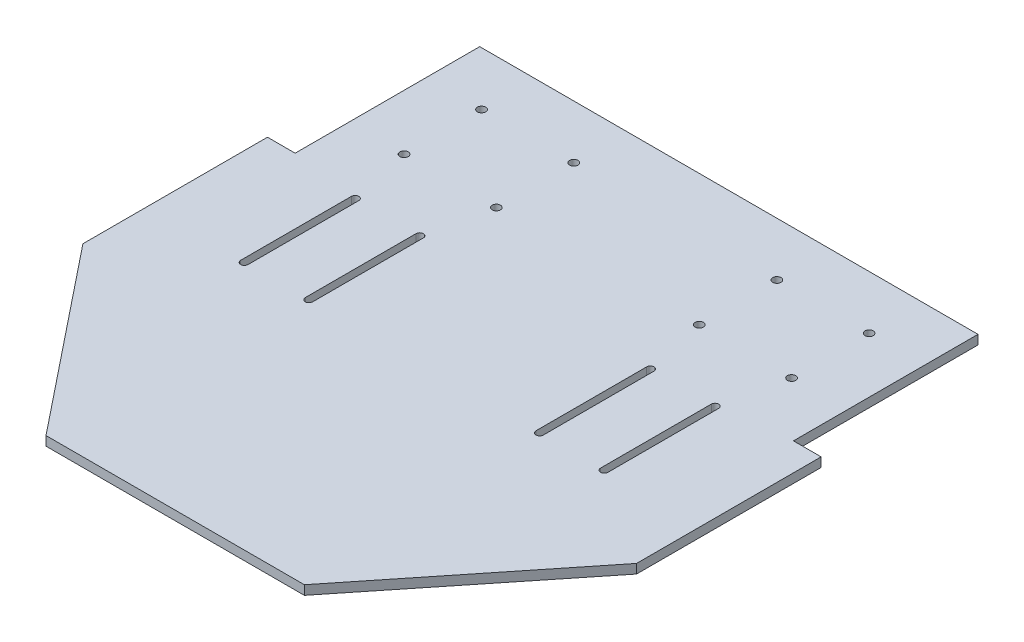
SolidWorks part; units mm, degrees
ref_plane "前基準面" through (0, 0, 0) normal (0, 0, 1) x (1, 0, 0)
ref_plane "上基準面" through (0, 0, 0) normal (0, 1, 0) x (1, 0, 0)
ref_plane "右基準面" through (0, 0, 0) normal (1, 0, 0) x (0, 0, -1)
sketch "草圖2" plane through (0, 0, 0) normal (0, 1, 0) x (1, 0, 0)
  line L0 (0, 150) -> (0, 0) construction
  line L1 (-150, 150) -> (150, 150)
  line L2 (-150, 150) -> (-150, -50)
  line L3 (-70, -150) -> (70, -150)
  line L4 (150, 150) -> (150, -50)
  line L5 (-150, 150) -> (150, -150) construction
  line L6 (-150, -150) -> (150, 150) construction
  line L7 (-105, 121) -> (-55, 121) construction
  line L8 (-105, 121) -> (-105, 79) construction
  line L9 (-105, 79) -> (-55, 79) construction
  line L10 (-55, 121) -> (-55, 79) construction
  line L11 (-105, 121) -> (-55, 79) construction
  line L12 (-105, 79) -> (-55, 121) construction
  line L13 (55, 121) -> (55, 79) construction
  line L14 (105, 79) -> (55, 79) construction
  line L15 (105, 121) -> (105, 79) construction
  line L16 (105, 121) -> (55, 121) construction
  line L17 (-150, -50) -> (-70, -150)
  line L18 (150, -50) -> (70, -150)
  line L19 (-150, -50) -> (-150, -150) construction
  line L20 (-150, -150) -> (-70, -150) construction
  line L21 (150, -50) -> (150, -150) construction
  line L22 (150, -150) -> (70, -150) construction
  circle A0 centre (-105, 121) radius 2.25
  circle A1 centre (-105, 79) radius 2.25
  circle A2 centre (-55, 79) radius 2.25
  circle A3 centre (-55, 121) radius 2.25
  circle A4 centre (55, 121) radius 2.25
  circle A5 centre (55, 79) radius 2.25
  circle A6 centre (105, 121) radius 2.25
  circle A7 centre (105, 79) radius 2.25
  point P0 (0, 0)
  point P6 (-80, 100)
  dimension "D7" = 4.5
  dimension "D1" = 42
  dimension "D2" = 50
  dimension "D3" = 50
  dimension "D4" = 70
  dimension "D5" = 300
  dimension "D6" = 300
  dimension "D8" = 100
  dimension "D9" = 80
extrude "填料-伸長2" add sketch "草圖2" along normal blind 5
sketch "草圖3" plane through (0, 5, 0) normal (0, 1, 0) x (1, 0, 0)
  line L0 (0, 150) -> (0, 0) construction
  line L1 (-150, 150) -> (-135, 150)
  line L2 (-150, 150) -> (-150, 50)
  line L3 (-150, 50) -> (-135, 50)
  line L4 (-135, 150) -> (-135, 50)
  line L5 (150, 150) -> (-150, 150) construction
  line L6 (135, 150) -> (135, 50)
  line L7 (150, 50) -> (135, 50)
  line L8 (150, 150) -> (150, 50)
  line L9 (150, 150) -> (135, 150)
  dimension "D1" = 15
  dimension "D2" = 100
extrude "除料-伸長1" cut sketch "草圖3" against normal blind 5
sketch "草圖4" plane through (0, 5, 0) normal (0, 1, 0) x (1, 0, 0)
  line L0 (-150.2953, 15) -> (161.001, 15) construction
  line L1 (-97.5, 35) -> (-62.5, 35) construction
  line L2 (-97.5, 35) -> (-97.5, -5) construction
  line L3 (-97.5, -5) -> (-62.5, -5) construction
  line L4 (-62.5, 35) -> (-62.5, -5) construction
  line L5 (-97.5, 35) -> (-62.5, -5) construction
  line L6 (-97.5, -5) -> (-62.5, 35) construction
  line L7 (-150, 50) -> (-150, -50) construction
  line L8 (-97.5, 45) -> (-97.5, -15) construction
  line L9 (-97.5, 45) -> (-97.5, -15) construction
  line L10 (-80, -5) -> (-80, 58.5317) construction
  line L11 (-95.5, 45) -> (-95.5, -15)
  line L12 (-99.5, 45) -> (-99.5, -15)
  line L13 (-62.5, 45) -> (-62.5, -15) construction
  line L14 (-64.5, 45) -> (-64.5, -15)
  line L15 (-60.5, 45) -> (-60.5, -15)
  line L16 (0, 60.0422) -> (0, -21.3854) construction
  line L17 (97.5, 45) -> (97.5, -15) construction
  line L18 (95.5, 45) -> (95.5, -15)
  line L19 (99.5, 45) -> (99.5, -15)
  line L20 (62.5, 45) -> (62.5, -15) construction
  line L21 (64.5, 45) -> (64.5, -15)
  line L22 (60.5, 45) -> (60.5, -15)
  arc A0 (-95.5, 45) -> (-99.5, 45) centre (-97.5, 45) ccw
  arc A1 (-99.5, -15) -> (-95.5, -15) centre (-97.5, -15) ccw
  arc A2 (-64.5, 45) -> (-60.5, 45) centre (-62.5, 45) cw
  arc A3 (-60.5, -15) -> (-64.5, -15) centre (-62.5, -15) cw
  arc A4 (95.5, 45) -> (99.5, 45) centre (97.5, 45) cw
  arc A5 (99.5, -15) -> (95.5, -15) centre (97.5, -15) cw
  arc A6 (64.5, 45) -> (60.5, 45) centre (62.5, 45) ccw
  arc A7 (60.5, -15) -> (64.5, -15) centre (62.5, -15) ccw
  point P0 (-80, 15)
  point P12 (-97.5, 15)
  point P21 (-62.5, 15)
  point P30 (97.5, 15)
  point P37 (62.5, 15)
  dimension "D7" = 2
  dimension "D1" = 40
  dimension "D2" = 35
  dimension "D3" = 15
  dimension "D4" = 70
  dimension "D5" = 10
  dimension "D6" = 10
extrude "除料-伸長2" cut sketch "草圖4" against normal blind 5
